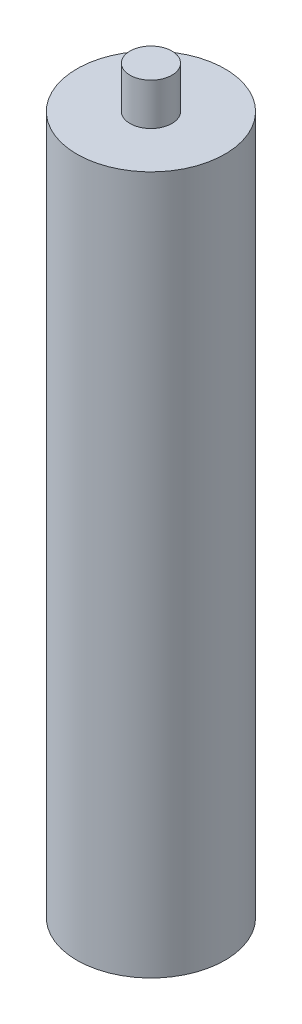
SolidWorks part; units mm, degrees
ref_plane "Front Plane" through (0, 0, 0) normal (0, 0, 1) x (1, 0, 0)
ref_plane "Top Plane" through (0, 0, 0) normal (0, 1, 0) x (1, 0, 0)
ref_plane "Right Plane" through (0, 0, 0) normal (1, 0, 0) x (0, 0, -1)
sketch "Sketch1" plane through (0, 0, 0) normal (0, 1, 0) x (1, 0, 0)
  circle A0 centre (0, 0) radius 26.5
  dimension "D1" = 53
extrude "Boss-Extrude1" add sketch "Sketch1" along normal blind 250
sketch "Sketch2" plane through (0, 250, 0) normal (0, 1, 0) x (1, 0, 0)
  circle A0 centre (0, 0) radius 7.5
  dimension "D1" = 15
extrude "Boss-Extrude2" add sketch "Sketch2" along normal blind 15
